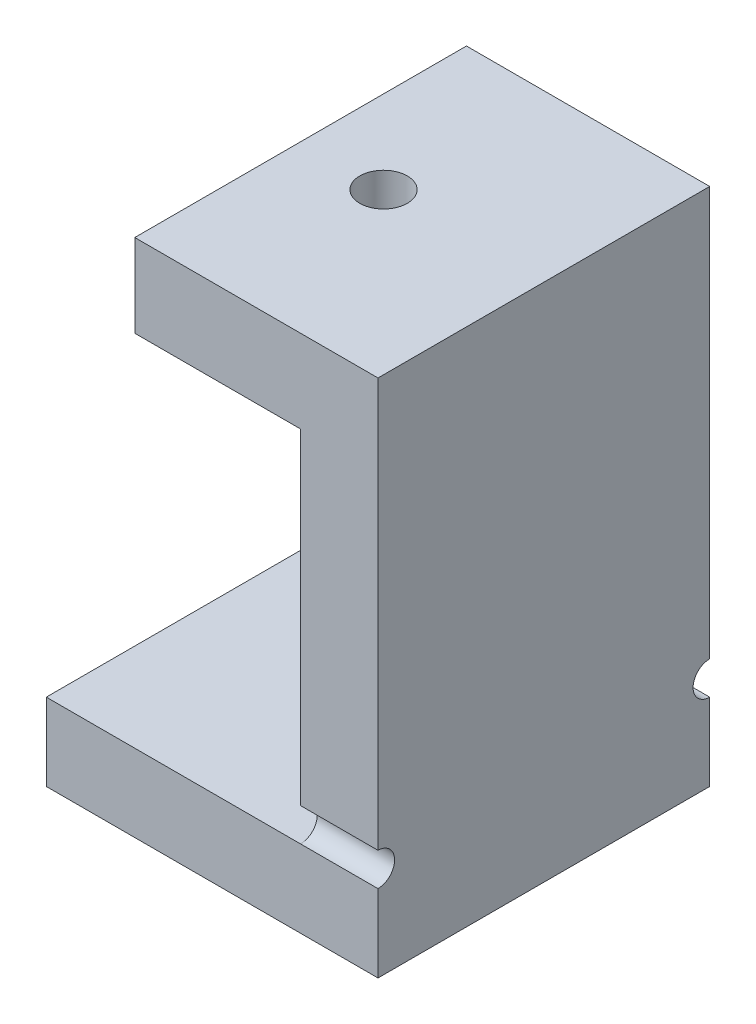
SolidWorks part; units mm, degrees
ref_plane "Front Plane" through (0, 0, 0) normal (0, 0, 1) x (1, 0, 0)
ref_plane "Top Plane" through (0, 0, 0) normal (0, 1, 0) x (1, 0, 0)
ref_plane "Right Plane" through (0, 0, 0) normal (1, 0, 0) x (0, 0, -1)
sketch "Sketch1" plane through (0, 0, 0) normal (0, 1, 0) x (1, 0, 0)
  line L1 (-15, 15) -> (15, 15)
  line L2 (-15, 15) -> (-15, -15)
  line L3 (-15, -15) -> (15, -15)
  line L4 (15, 15) -> (15, -15)
  line L5 (-15, 15) -> (15, -15) construction
  line L6 (-15, -15) -> (15, 15) construction
  point P0 (0, 0)
  dimension "D1" = 30
  dimension "D2" = 30
extrude "Boss-Extrude1" add sketch "Sketch1" along normal blind 7
sketch "Sketch2" plane through (0, 7, 0) normal (0, 1, 0) x (1, 0, 0)
  line L0 (-15, -15) -> (15, -15) construction
  line L1 (15, 15) -> (8, 15)
  line L2 (15, 15) -> (15, -15)
  line L3 (15, -15) -> (8, -15)
  line L4 (8, 15) -> (8, -15)
  dimension "D1" = 7
extrude "Boss-Extrude2" add sketch "Sketch2" along normal blind 40
sketch "Sketch3" plane through (8, 0, 0) normal (-1, 0, 0) x (0, 0, 1)
  line L0 (-15, 47) -> (-15, 7) construction
  line L1 (15, 47) -> (-15, 47)
  line L2 (15, 47) -> (15, 39.5)
  line L3 (15, 39.5) -> (-15, 39.5)
  line L4 (-15, 47) -> (-15, 39.5)
  dimension "D1" = 7.5
extrude "Boss-Extrude3" add sketch "Sketch3" along normal blind 15
sketch "Sketch4" plane through (0, 39.5, 0) normal (0, -1, 0) x (1, 0, 0)
  line L1 (8, -15) -> (8, 15) construction
  line L2 (0.5, -4.3301) -> (4.25, -2.1651)
  line L3 (4.25, -2.1651) -> (4.25, 2.1651)
  line L4 (4.25, 2.1651) -> (0.5, 4.3301)
  line L5 (0.5, 4.3301) -> (-3.25, 2.1651)
  line L6 (-3.25, 2.1651) -> (-3.25, -2.1651)
  line L7 (-3.25, -2.1651) -> (0.5, -4.3301)
  circle A0 centre (0.5, 0) radius 3.75 construction
  dimension "D1" = 7.5
  dimension "D2" = 7.5
extrude "Cut-Extrude1" cut sketch "Sketch4" against normal blind 2.5
hole_wizard "M4 Clearance Hole1" positions "Sketch7" profile "Sketch6" hole size "M4" standard "DIN"
sketch "Sketch7" plane through (0, 47, 0) normal (0, 1, 0) x (-1, 0, 0)
  line L0 (3.25, 2.1651) -> (3.25, -2.1651) construction
  line L1 (-4.25, -2.1651) -> (-4.25, 2.1651) construction
  line L2 (3.25, 2.1651) -> (3.25, -2.1651)
  line L3 (-4.25, -2.1651) -> (-4.25, 2.1651)
  line L4 (3.25, 0) -> (-4.25, 0) construction
  point P0 (-0.5, 0)
sketch "Sketch6" plane through (0.5, 47, 0) normal (1, 0, 0) x (0, 0, 1)
  line L0 (0, 0) -> (0, 7.2919)
  line L1 (0, 7.2919) -> (2.15, 6)
  line L2 (2.15, 6) -> (2.15, 0)
  line L5 (2.15, 0) -> (0, 0)
  line L10 (0, 7.2919) -> (-2.15, 6) construction
  line L11 (0, -6.35) -> (0, 107.95) construction
  dimension "Hole Dia." = 4.3
  dimension "Hole Depth" = 6
  dimension "Drill Angle" = 118
sketch "Sketch8" plane through (15, 0, 0) normal (1, 0, 0) x (0, 0, -1)
  line L0 (-15, 47) -> (-15, 0) construction
  line L1 (-15, 10) -> (-15, 7)
  line L2 (0, 0) -> (0, 15.9269) construction
  line L3 (-15, 0) -> (15, 0) construction
  line L4 (15, 10) -> (15, 7)
  arc A0 (-15, 7) -> (-15, 10) centre (-15, 8.5) ccw
  arc A1 (15, 7) -> (15, 10) centre (15, 8.5) cw
  dimension "D2" = 1.5
  dimension "D1" = 7
extrude "Cut-Extrude3" cut sketch "Sketch8" against normal blind 13
